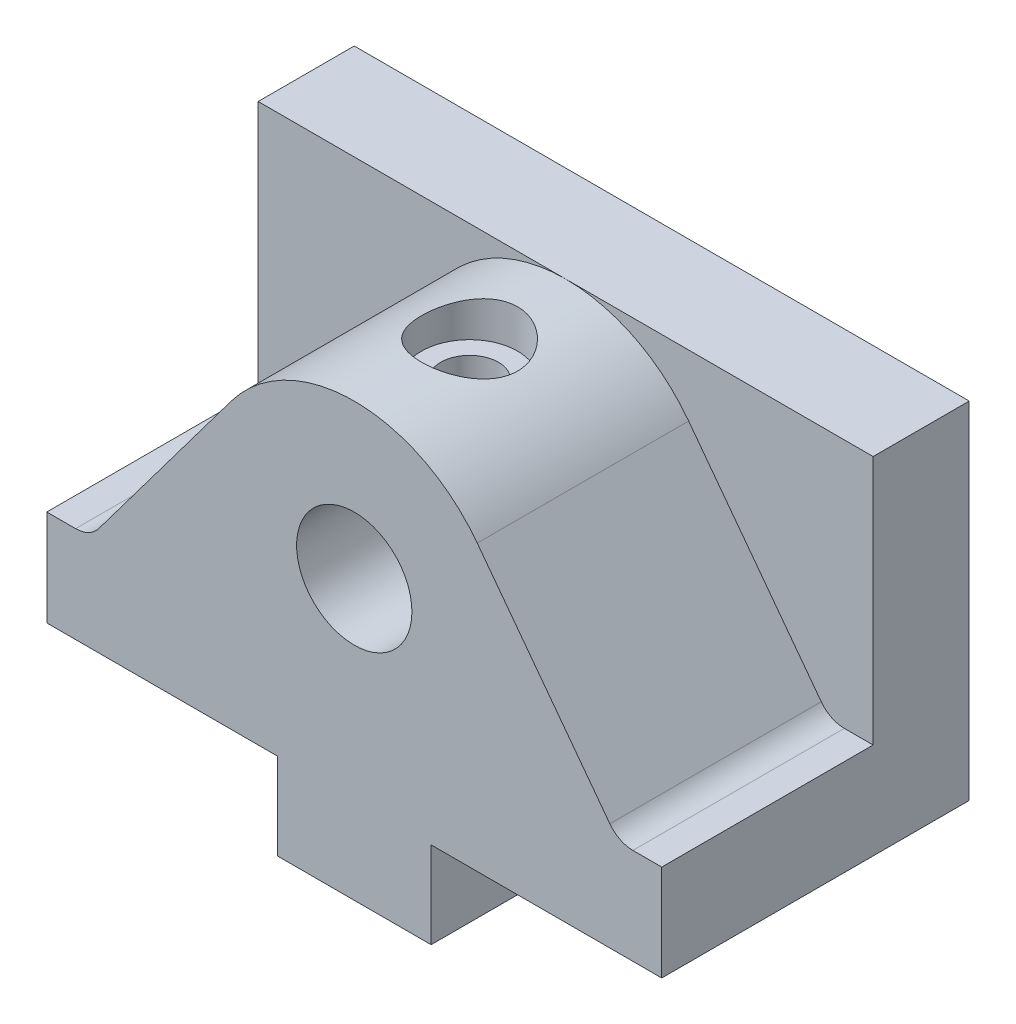
SolidWorks part; units mm, degrees
ref_plane "Front Plane" through (0, 0, 0) normal (0, 0, 1) x (1, 0, 0)
ref_plane "Top Plane" through (0, 0, 0) normal (0, 1, 0) x (1, 0, 0)
ref_plane "Right Plane" through (0, 0, 0) normal (1, 0, 0) x (0, 0, -1)
sketch "Sketch1" plane through (0, 0, 0) normal (0, 0, 1) x (1, 0, 0)
  line L0 (40, 0) -> (64, 0)
  line L1 (0, 0) -> (24, 0)
  line L2 (0, 0) -> (0, 36)
  line L3 (0, 36) -> (64, 36)
  line L4 (64, 0) -> (64, 36)
  line L6 (24, 0) -> (24, -9)
  line L7 (24, -9) -> (40, -9)
  line L8 (40, 0) -> (40, -9)
  line L9 (32, 50.9753) -> (32, -43.9842) construction
  point P9 (32, -9)
  dimension "D1" = 64
  dimension "D2" = 36
  dimension "D3" = 16
  dimension "D4" = 9
extrude "Boss-Extrude1" add sketch "Sketch1" along normal blind 32
sketch "Sketch2" plane through (0, 0, 32) normal (0, 0, 1) x (1, 0, 0)
  line L0 (24, -9) -> (40, -9) construction
  line L1 (64, 0) -> (64, 36) construction
  line L2 (0, 36) -> (0, 0) construction
  line L3 (0, 10) -> (3, 10)
  line L4 (0, 0) -> (24, 0) construction
  line L5 (64, 36) -> (0, 36) construction
  line L6 (64, 10) -> (64, 36)
  line L7 (64, 36) -> (0, 36)
  line L8 (19.2, 29.6) -> (5.4, 11.2)
  line L9 (44.8, 29.6) -> (58.6, 11.2)
  line L10 (32, -12.3891) -> (32, 1.4951) construction
  line L11 (0, 36) -> (0, 10)
  line L12 (61, 10) -> (64, 10)
  arc A0 (44.8, 29.6) -> (19.2, 29.6) centre (32, 20) ccw
  circle A1 centre (32, 20) radius 6
  arc A2 (61, 10) -> (58.6, 11.2) centre (61, 13) cw
  arc A3 (5.4, 11.2) -> (3, 10) centre (3, 13) cw
  point P6 (32, -9)
  point P23 (59.5, 10)
  point P26 (4.5, 10)
  line M7 (0, 36) -> (0, 0)
  line M13 (64, 0) -> (64, 36)
  line M14 (64, 36) -> (0, 36)
  dimension "D1" = 32
  dimension "D2" = 12
  dimension "D5" = 3
  dimension "D3" = 10
  dimension "D4" = 55
extrude "Cut-Extrude1" cut sketch "Sketch2" against normal blind 22 contours A3 L8 A0 L7 L3 M7 | A2 L12 A0 L9 M13 M14 | A1
sketch "Sketch3" plane through (0, 36, 0) normal (0, 1, 0) x (1, 0, 0)
  line L1 (64, 0) -> (0, 0) construction
  circle A0 centre (32, -20) radius 5
  point P2 (0, 0)
  dimension "D1" = 10
  dimension "D2" = 20
extrude "Cut-Extrude2" cut sketch "Sketch3" against normal blind 4
sketch "Sketch4" plane through (0, 32, 0) normal (0, 1, 0) x (1, 0, 0)
  circle A0 centre (32, -20) radius 3
  dimension "D1" = 6
extrude "Cut-Extrude3" cut sketch "Sketch4" against normal up to next and the other way through all
sketch "Sketch5" plane through (0, -9, 0) normal (0, -1, 0) x (1, 0, 0)
  line L0 (24, 32) -> (40, 32) construction
  line L1 (64, 32) -> (64, 0) construction
  circle A0 centre (32, 24) radius 3
  circle A1 centre (32, 8) radius 3
  point P8 (0, 0)
  dimension "D1" = 8
  dimension "D4" = 6
  dimension "D2" = 16
  dimension "D3" = 32
extrude "Cut-Extrude4" cut sketch "Sketch5" against normal blind 16
